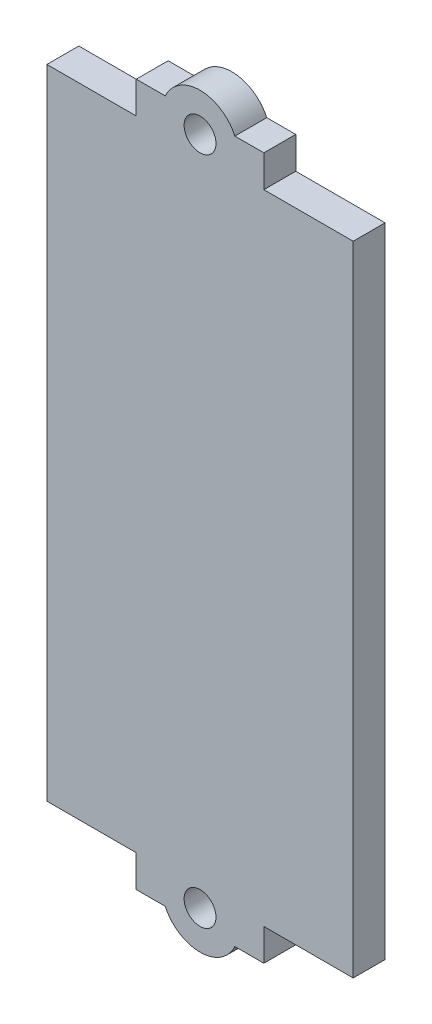
SolidWorks part; units mm, degrees
ref_plane "Front Plane" through (0, 0, 0) normal (0, 0, 1) x (1, 0, 0)
ref_plane "Top Plane" through (0, 0, 0) normal (0, 1, 0) x (1, 0, 0)
ref_plane "Right Plane" through (0, 0, 0) normal (1, 0, 0) x (0, 0, -1)
sketch "Sketch1" plane through (0, 0, 0) normal (0, 0, 1) x (1, 0, 0)
  line L1 (24, 50) -> (-24, 50)
  line L2 (24, 50) -> (24, -50)
  line L3 (24, -50) -> (-24, -50)
  line L4 (-24, 50) -> (-24, -50)
  line L5 (24, 50) -> (-24, -50) construction
  line L6 (24, -50) -> (-24, 50) construction
  point P0 (0, 0)
  dimension "D1" = 48
  dimension "D2" = 100
extrude "Boss-Extrude1" add sketch "Sketch1" along normal blind 5
sketch "Sketch2" plane through (0, 50, 0) normal (0, 1, 0) x (1, 0, 0)
  line L0 (24, -5) -> (-24, -5) construction
  line L1 (-10, -5) -> (10, -5)
  line L2 (-10, -5) -> (-10, 0)
  line L3 (-10, 0) -> (10, 0)
  line L4 (10, -5) -> (10, 0)
  line L5 (24, 0) -> (-24, 0) construction
  line L6 (-24, -5) -> (-24, 0) construction
  line L8 (24, -5) -> (24, 0) construction
  dimension "D1" = 14
  dimension "D2" = 20
  dimension "D3" = 14
  dimension "D4" = 5
extrude "Boss-Extrude2" add sketch "Sketch2" along normal blind 5
mirror "Mirror1" about plane through (0, 0, 0) normal (0, 1, 0) of "Boss-Extrude2"
sketch "Sketch3" plane through (0, 0, 5) normal (0, 0, 1) x (1, 0, 0)
  line L0 (-10, 55) -> (10, 55) construction
  line L1 (-10, 50) -> (-24, 50) construction
  line L2 (10, 55) -> (10, 50) construction
  line L3 (-10, 55) -> (-10, 50) construction
  circle A0 centre (0, 52.5) radius 6
  dimension "D1" = 12
  dimension "D2" = 2.5
  dimension "D3" = 10
  dimension "D4" = 2.5
  dimension "D5" = 10
extrude "Boss-Extrude3" add sketch "Sketch3" against normal blind 5
sketch "Sketch4" plane through (0, 0, 5) normal (0, 0, 1) x (1, 0, 0)
  line L0 (10, 55) -> (10, 50) construction
  line L1 (5.4544, 55) -> (10, 55) construction
  circle A0 centre (0, 52.5) radius 2.5
  arc A2 (5.4544, 55) -> (-5.4544, 55) centre (0, 52.5) ccw construction
  dimension "D1" = 5
  dimension "D2" = 10
  dimension "D3" = 2.5
  dimension "D4" = 3.5
extrude "Cut-Extrude1" cut sketch "Sketch4" against normal blind 5
mirror "Mirror2" about plane through (0, 0, 0) normal (0, 1, 0) of "Boss-Extrude3", "Cut-Extrude1"
